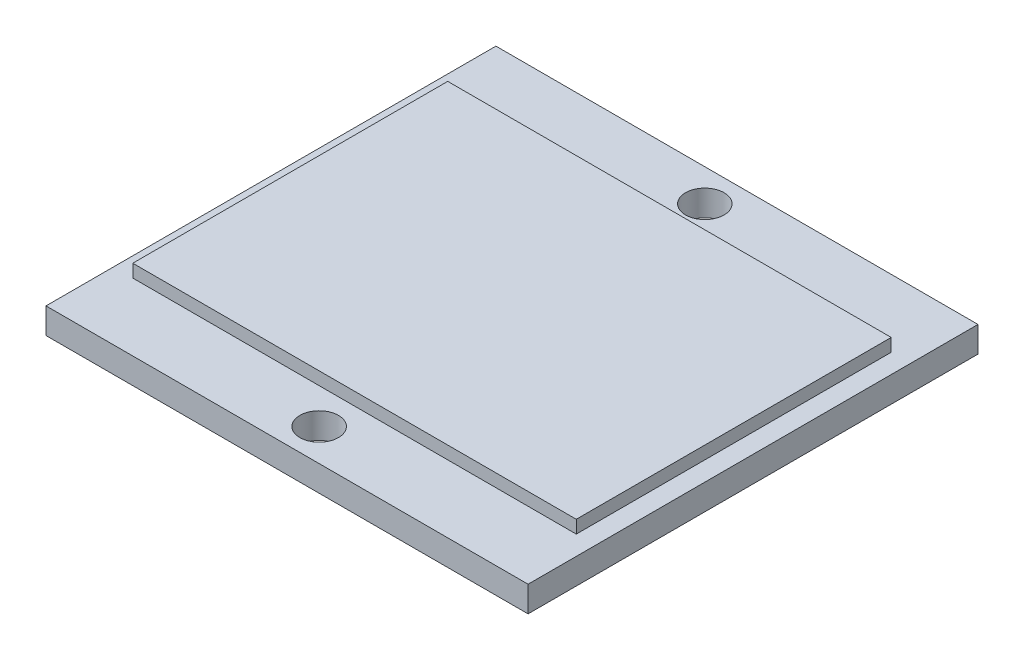
SolidWorks part; units mm, degrees
ref_plane "Front Plane" through (0, 0, 0) normal (0, 0, 1) x (1, 0, 0)
ref_plane "Top Plane" through (0, 0, 0) normal (0, 1, 0) x (1, 0, 0)
ref_plane "Right Plane" through (0, 0, 0) normal (1, 0, 0) x (0, 0, -1)
sketch "Sketch1" plane through (0, 0, 0) normal (0, 1, 0) x (1, 0, 0)
  line L1 (-24.9278, 19.3476) -> (50.0722, 19.3476)
  line L2 (-24.9278, 19.3476) -> (-24.9278, -50.6524)
  line L3 (-24.9278, -50.6524) -> (50.0722, -50.6524)
  line L4 (50.0722, 19.3476) -> (50.0722, -50.6524)
  dimension "D1" = 70
  dimension "D2" = 75
extrude "Boss-Extrude1" add sketch "Sketch1" along normal blind 4
sketch "Sketch2" plane through (0, 4, 0) normal (0, 1, 0) x (1, 0, 0)
  line L0 (-24.9278, 19.3476) -> (-24.9278, -50.6524) construction
  line L1 (-21.9278, -40.1524) -> (47.0722, -40.1524)
  line L2 (-21.9278, -40.1524) -> (-21.9278, 8.8476)
  line L3 (-21.9278, 8.8476) -> (47.0722, 8.8476)
  line L4 (47.0722, -40.1524) -> (47.0722, 8.8476)
  line L5 (50.0722, 19.3476) -> (-24.9278, 19.3476) construction
  point P4 (-24.9278, -15.6524)
  point P5 (12.5722, 19.3476)
  point P8 (12.5722, 8.8476)
  point P11 (-21.9278, -15.6524)
  dimension "D1" = 69
  dimension "D2" = 49
extrude "Boss-Extrude2" add sketch "Sketch2" along normal blind 2
sketch "Sketch3" plane through (0, 4, 0) normal (0, 1, 0) x (1, 0, 0)
  line L0 (50.0722, 19.3476) -> (-24.9278, 19.3476) construction
  line L1 (50.0722, -50.6524) -> (50.0722, 19.3476) construction
  circle A0 centre (12.5722, 14.3476) radius 3
  circle A1 centre (12.5722, -45.6524) radius 3
  point P0 (12.5722, 19.3476)
  point P7 (50.0722, -15.6524)
  dimension "D1" = 6
  dimension "D2" = 60
  dimension "D3" = 30
extrude "Cut-Extrude1" cut sketch "Sketch3" against normal blind 4
